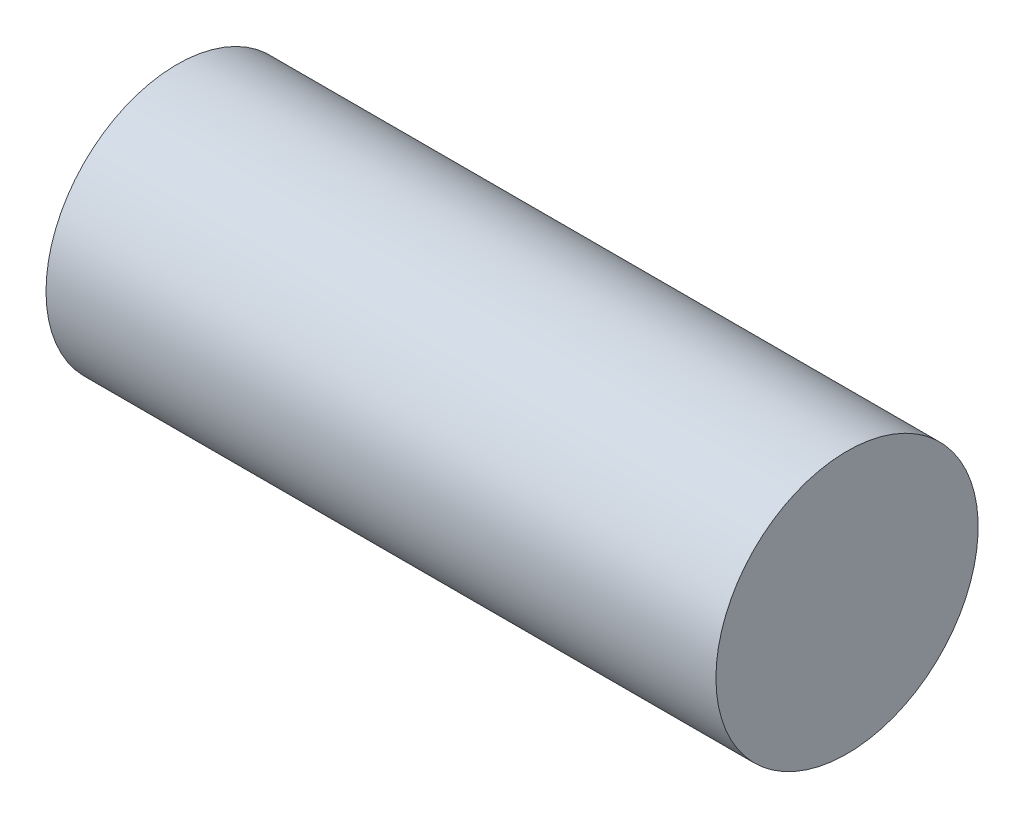
SolidWorks part; units mm, degrees
ref_plane "Front Plane" through (0, 0, 0) normal (0, 0, 1) x (1, 0, 0)
ref_plane "Top Plane" through (0, 0, 0) normal (0, 1, 0) x (1, 0, 0)
ref_plane "Right Plane" through (0, 0, 0) normal (1, 0, 0) x (0, 0, -1)
sketch "Sketch1" plane through (0, 0, 0) normal (0, 0, 1) x (1, 0, 0)
  line L0 (-44.0714, 0) -> (0, 0) construction
  line L1 (76.2, 0) -> (88.9, 0)
  line L2 (0, 9.525) -> (0, 17.399)
  line L3 (0, 17.399) -> (88.9, 17.399)
  line L4 (88.9, 0) -> (88.9, 17.399)
  line L5 (0, 9.525) -> (76.2, 9.525)
  line L6 (76.2, 9.525) -> (76.2, 0)
  line L7 (76.2, 0) -> (143.3988, 0) construction
  line L8 (0, -11.0445) -> (0, 43.0005) construction
  point P12 (93.0162, 21.082)
  dimension "D1" = 88.9
  dimension "D2" = 34.798
  dimension "D3" = 19.05
  dimension "D4" = 76.2
revolve "Revolve1" add sketch "Sketch1" angle 360 about L0
